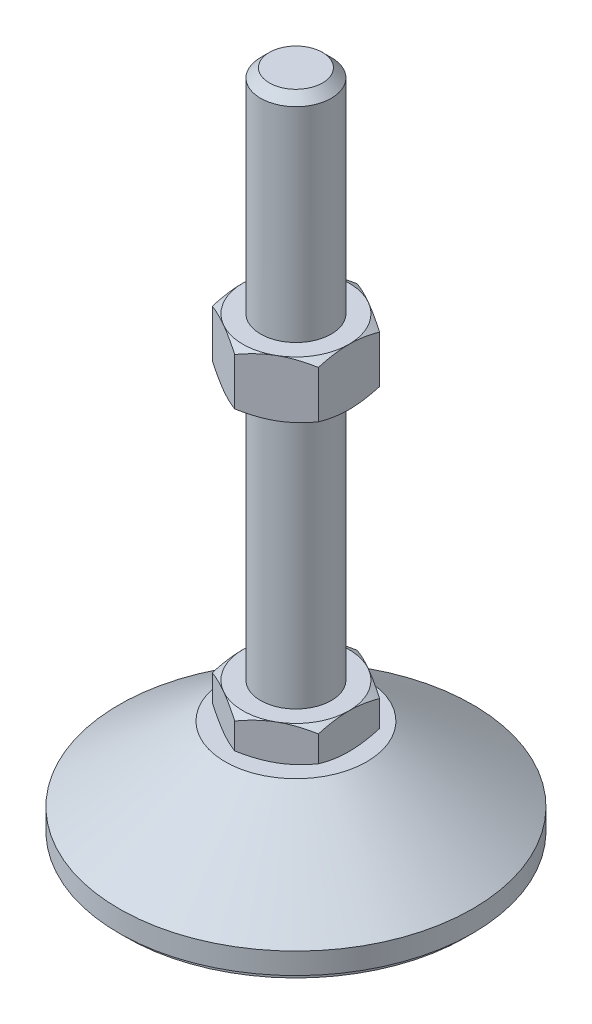
SolidWorks part; units mm, degrees
ref_plane "Спереди" through (0, 0, 0) normal (0, 0, 1) x (1, 0, 0)
ref_plane "Сверху" through (0, 0, 0) normal (0, 1, 0) x (1, 0, 0)
ref_plane "Справа" through (0, 0, 0) normal (1, 0, 0) x (0, 0, -1)
sketch "Эскиз1" plane through (0, 0, 0) normal (0, 0, 1) x (1, 0, 0)
  line L0 (0, 0) -> (-48, 0)
  line L1 (-48, 0) -> (-48, 2)
  line L2 (-48, 2) -> (-50, 2)
  line L3 (-50, 2) -> (-50, 8)
  line L4 (-50, 8) -> (-20, 29)
  line L5 (-20, 29) -> (-10, 29)
  line L12 (-10, 39) -> (-10, 186.5)
  line L13 (-10, 186.5) -> (-7.5, 189)
  line L14 (-7.5, 189) -> (0, 189)
  line L15 (0, 189) -> (0, 0) construction
  line L16 (-10, 29) -> (0, 29) construction
  line L17 (0, 0) -> (0, 189)
  line L18 (0, 0) -> (0, -7.9595) construction
  line L19 (-10, 39) -> (-10, 29)
  point P8 (-10, 112.75)
  point P23 (-15, 29)
  dimension "D1" = 20
  dimension "D2" = 29
  dimension "D3" = 10
  dimension "D4" = 100
  dimension "D5" = 10
  dimension "D6" = 2.5
  dimension "D7" = 45
  dimension "D8" = 40
  dimension "D9" = 2
  dimension "D10" = 150
  dimension "D11" = 6
revolve "Повернуть1" add sketch "Эскиз1" angle 360 about L17
sketch "Эскиз2" plane through (0, 29, 0) normal (0, 1, 0) x (1, 0, 0)
  line L1 (0, 17.3205) -> (-15, 8.6603)
  line L2 (-15, 8.6603) -> (-15, -8.6603)
  line L3 (-15, -8.6603) -> (0, -17.3205)
  line L4 (0, -17.3205) -> (15, -8.6603)
  line L5 (15, -8.6603) -> (15, 8.6603)
  line L6 (15, 8.6603) -> (0, 17.3205)
  circle A0 centre (0, 0) radius 15 construction
  dimension "D1" = 30
extrude "Бобышка-Вытянуть1" add sketch "Эскиз2" along normal up to vertex (10 mm away) up to point (-10, 39, 0)
ref_plane "Плоскость1" through (0, 112.75, 0) normal (0, 1, 0) x (1, 0, 0)
sketch "Эскиз3" plane through (0, 112.75, 0) normal (0, 1, 0) x (1, 0, 0)
  line L6 (15, 8.6603) -> (0, 17.3205)
  line L7 (0, 17.3205) -> (-15, 8.6603)
  line L8 (-15, 8.6603) -> (-15, -8.6603)
  line L9 (-15, -8.6603) -> (0, -17.3205)
  line L10 (0, -17.3205) -> (15, -8.6603)
  line L11 (15, -8.6603) -> (15, 8.6603)
  line L12 (15, 8.6603) -> (0, 17.3205)
  line L13 (0, 17.3205) -> (-15, 8.6603)
  line L14 (-15, 8.6603) -> (-15, -8.6603)
  line L15 (-15, -8.6603) -> (0, -17.3205)
  line L16 (0, -17.3205) -> (15, -8.6603)
  line L17 (15, -8.6603) -> (15, 8.6603)
  dimension "D1" = 0
extrude "Бобышка-Вытянуть2" add sketch "Эскиз3" along normal blind 16
sketch "Эскиз4" plane through (0, 0, 0) normal (0, 0, 1) x (1, 0, 0)
  line L0 (-15, 128.75) -> (-28.8564, 120.75)
  line L1 (-28.8564, 120.75) -> (-28.8564, 128.75)
  line L2 (-28.8564, 128.75) -> (-15, 128.75)
  line L3 (-28.8564, 120.75) -> (-15, 112.75)
  line L4 (50, 112.75) -> (-50, 112.75) construction
  line L5 (-15, 112.75) -> (-28.8564, 112.75)
  line L6 (-28.8564, 112.75) -> (-28.8564, 120.75)
  line L7 (-15, 128.75) -> (-15, 112.75) construction
  line L8 (-15, 39) -> (-23.6603, 39)
  line L9 (-23.6603, 39) -> (-23.6603, 34)
  line L10 (-23.6603, 34) -> (-15, 39)
  line L11 (-15, 29) -> (-23.6603, 34)
  line L12 (-23.6603, 34) -> (-23.6603, 29)
  line L13 (-23.6603, 29) -> (-15, 29)
  line L14 (0, 189) -> (0, 96.3793) construction
  dimension "D1" = 30
  dimension "D2" = 30
revolve "Вырез-Повернуть2" cut sketch "Эскиз4" angle 360 about L14
